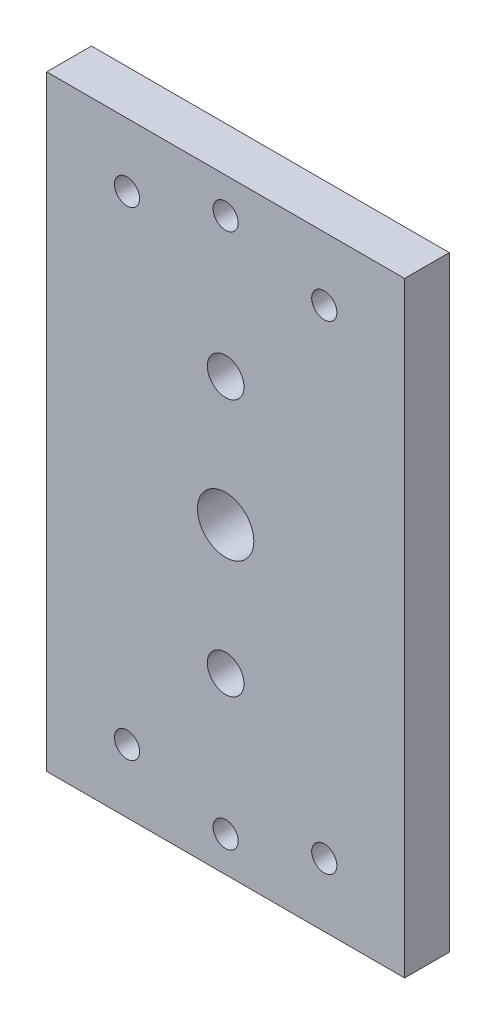
SolidWorks part; units mm, degrees
material "6061-O (SS)"
ref_plane "Alzado" through (0, 0, 0) normal (0, 0, 1) x (1, 0, 0)
ref_plane "Planta" through (0, 0, 0) normal (0, 1, 0) x (1, 0, 0)
ref_plane "Vista lateral" through (0, 0, 0) normal (1, 0, 0) x (0, 0, -1)
sketch "Croquis1" plane through (0, 0, 0) normal (0, 0, 1) x (1, 0, 0)
  line L1 (0, 0) -> (50.8, 0)
  line L2 (0, 0) -> (0, 86)
  line L3 (0, 86) -> (50.8, 86)
  line L4 (50.8, 0) -> (50.8, 86)
  dimension "D1" = 50.8
  dimension "D2" = 86
extrude "Saliente-Extruir1" add sketch "Croquis1" along normal blind 6.35
sketch "Croquis2" plane through (0, 0, 6.35) normal (0, 0, 1) x (1, 0, 0)
  line L0 (50.8, 86) -> (0, 86) construction
  line L1 (50.8, 0) -> (50.8, 86) construction
  line L2 (43.65, 43) -> (7.15, 43) construction
  line L3 (25.4, 61.25) -> (25.4, 24.75) construction
  circle A0 centre (25.4, 43) radius 4
  circle A3 centre (25.4, 61.25) radius 2.6
  circle A4 centre (25.4, 24.75) radius 2.6
  point P5 (25.4, 86)
  point P8 (50.8, 43)
  point P12 (25.4, 43)
  point P17 (25.4, 43)
  dimension "D1" = 8
  dimension "D5" = 5.2
  dimension "D6" = 5.2
  dimension "D4" = 36.5
  dimension "D7" = 41.7
extrude "Cortar-Extruir1" cut sketch "Croquis2" against normal blind 6.35
sketch "Croquis3" plane through (0, 0, 6.35) normal (0, 0, 1) x (1, 0, 0)
  line L0 (11.4, 77) -> (39.4, 77) construction
  line L1 (50.8, 86) -> (0, 86) construction
  line L2 (0, 43) -> (50.8, 43) construction
  line L3 (0, 86) -> (0, 0) construction
  line L4 (50.8, 0) -> (50.8, 86) construction
  circle A0 centre (25.4, 81) radius 1.785
  circle A1 centre (11.4, 77) radius 1.785
  circle A2 centre (39.4, 77) radius 1.785
  circle A3 centre (39.4, 9) radius 1.785
  circle A4 centre (11.4, 9) radius 1.785
  circle A5 centre (25.4, 5) radius 1.785
  point P6 (25.4, 77)
  point P9 (25.4, 86)
  dimension "D1" = 3.57
  dimension "D2" = 3.57
  dimension "D5" = 3.57
  dimension "D3" = 4
  dimension "D4" = 5
  dimension "D6" = 28
extrude "Cortar-Extruir2" cut sketch "Croquis3" against normal through all
